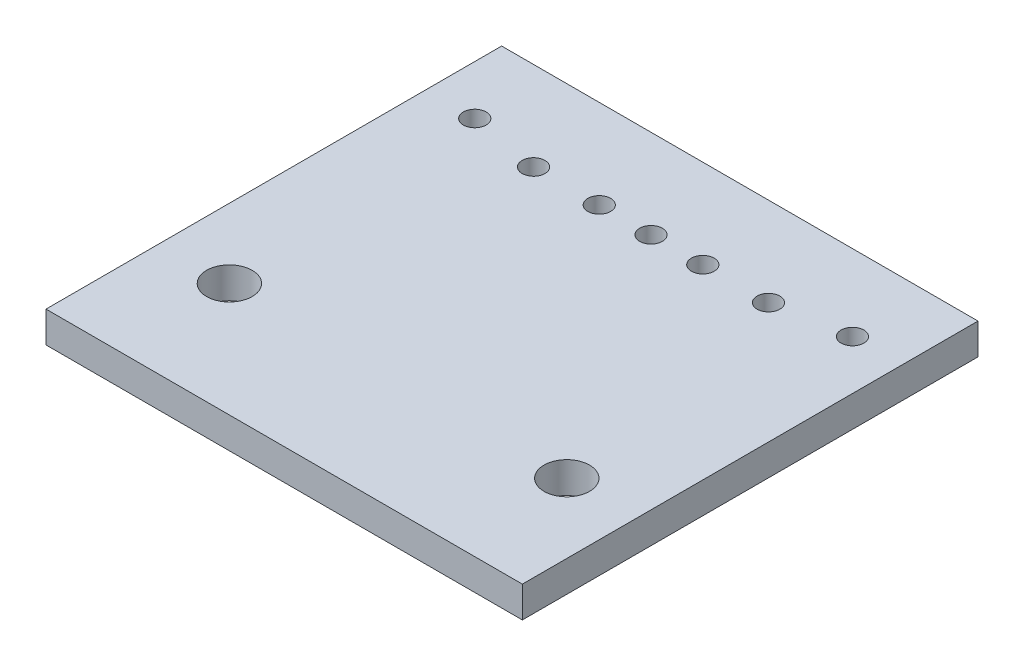
SolidWorks part; units mm, degrees
ref_plane "Front Plane" through (0, 0, 0) normal (0, 0, 1) x (1, 0, 0)
ref_plane "Top Plane" through (0, 0, 0) normal (0, 1, 0) x (1, 0, 0)
ref_plane "Right Plane" through (0, 0, 0) normal (1, 0, 0) x (0, 0, -1)
sketch "Sketch1" plane through (0, 0, 0) normal (0, 1, 0) x (1, 0, 0)
  line L1 (-11.5, -11) -> (11.5, -11)
  line L2 (-11.5, -11) -> (-11.5, 11)
  line L3 (-11.5, 11) -> (11.5, 11)
  line L4 (11.5, -11) -> (11.5, 11)
  line L5 (-11.5, -11) -> (11.5, 11) construction
  line L6 (-11.5, 11) -> (11.5, -11) construction
  point P0 (0, 0)
  dimension "D1" = 23
  dimension "D2" = 22
extrude "Boss-Extrude1" add sketch "Sketch1" along normal blind 1.5
sketch "Sketch2" plane through (0, 0, 0) normal (0, -1, 0) x (1, 0, 0)
  circle A0 centre (-8.1451, 5.5) radius 0.875 construction
  circle A1 centre (8.1451, 5.5) radius 0.875 construction
  circle A4 centre (-8.1451, 5.5) radius 0.875
  circle A5 centre (8.1451, 5.5) radius 0.875
  spline S0 degree 3 poles (-8.0835, -7.431) (-8.1588, -7.0042) (-8.2057, -6.866) (-8.3382, -6.6139) (-8.4259, -6.4966) (-8.6365, -6.3036) (-8.762, -6.2261) (-8.9642, -6.158) (-9.0356, -6.1427) (-9.1788, -6.1307) (-9.25, -6.1336) (-9.4629, -6.1699) (-9.5982, -6.2321) (-9.824, -6.4097) (-9.9158, -6.5248) (-10.0497, -6.7794) (-10.0923, -6.9184) (-10.1318, -7.2048) (-10.1286, -7.3483) (-10.0791, -7.6331) (-10.0337, -7.7687) (-9.9006, -8.024) (-9.8145, -8.1396) (-9.6041, -8.3341) (-9.4799, -8.4121) (-9.2737, -8.4821) (-9.2037, -8.4971) (-9.0612, -8.5095) (-8.9877, -8.5067) (-8.7754, -8.4707) (-8.6403, -8.4091) (-8.4131, -8.2308) (-8.321, -8.1151) (-8.12, -7.7325) (-8.0835, -7.431) (-8.1588, -7.0042) (-8.2057, -6.866) knots -0.125 -0.125 0 0 0.0625 0.0625 0.125 0.125 0.1875 0.1875 0.21875 0.21875 0.25 0.25 0.3125 0.3125 0.375 0.375 0.4375 0.4375 0.5 0.5 0.5625 0.5625 0.625 0.625 0.6875 0.6875 0.71875 0.71875 0.75 0.75 0.8125 0.8125 0.875 0.875 1 1 1.0625 1.0625 1.125 only from (-8.1337, -7.1465) to (-8.1337, -7.1465) construction
  spline S1 degree 3 poles (-4.6367, -6.8232) (-4.712, -6.3964) (-4.7588, -6.2582) (-4.8914, -6.0061) (-4.9791, -5.8889) (-5.1897, -5.6958) (-5.3152, -5.6183) (-5.5174, -5.5502) (-5.5888, -5.535) (-5.7319, -5.5229) (-5.8032, -5.5258) (-6.0161, -5.5621) (-6.1514, -5.6244) (-6.3772, -5.8019) (-6.469, -5.917) (-6.6029, -6.1717) (-6.6455, -6.3107) (-6.685, -6.597) (-6.6818, -6.7405) (-6.6322, -7.0253) (-6.5869, -7.1609) (-6.4538, -7.4162) (-6.3677, -7.5319) (-6.1573, -7.7264) (-6.0331, -7.8044) (-5.8269, -7.8744) (-5.7569, -7.8893) (-5.6144, -7.9017) (-5.5408, -7.8989) (-5.3286, -7.8629) (-5.1935, -7.8013) (-4.9663, -7.6231) (-4.8741, -7.5074) (-4.6732, -7.1248) (-4.6367, -6.8232) (-4.712, -6.3964) (-4.7588, -6.2582) knots -0.125 -0.125 0 0 0.0625 0.0625 0.125 0.125 0.1875 0.1875 0.21875 0.21875 0.25 0.25 0.3125 0.3125 0.375 0.375 0.4375 0.4375 0.5 0.5 0.5625 0.5625 0.625 0.625 0.6875 0.6875 0.71875 0.71875 0.75 0.75 0.8125 0.8125 0.875 0.875 1 1 1.0625 1.0625 1.125 only from (-4.6869, -6.5387) to (-4.6869, -6.5387) construction
  spline S2 degree 3 poles (8.1588, -7.0042) (8.1086, -7.2887) (8.1052, -7.4312) (8.1434, -7.7162) (8.1849, -7.8539) (8.3163, -8.1082) (8.4064, -8.2237) (8.5761, -8.3595) (8.6367, -8.3974) (8.7662, -8.4576) (8.8362, -8.48) (9.0476, -8.5186) (9.1954, -8.5069) (9.4695, -8.4173) (9.5955, -8.3403) (9.9149, -8.0501) (10.0524, -7.7785) (10.1279, -7.3564) (10.1318, -7.2099) (10.0942, -6.927) (10.0523, -6.7867) (9.9208, -6.5321) (9.8294, -6.4158) (9.6071, -6.2373) (9.4728, -6.1735) (9.1896, -6.1215) (9.0405, -6.1335) (8.7668, -6.2233) (8.6408, -6.3003) (8.4278, -6.4942) (8.34, -6.6109) (8.2051, -6.8667) (8.1588, -7.0042) (8.1086, -7.2887) (8.1052, -7.4312) knots -0.0625 -0.0625 0 0 0.0625 0.0625 0.125 0.125 0.1875 0.1875 0.21875 0.21875 0.25 0.25 0.3125 0.3125 0.375 0.375 0.5 0.5 0.5625 0.5625 0.625 0.625 0.6875 0.6875 0.75 0.75 0.8125 0.8125 0.875 0.875 0.9375 0.9375 1 1 1.0625 1.0625 1.125 only from (8.1337, -7.1465) to (8.1337, -7.1465) construction
  spline S3 degree 3 poles (4.737, -6.2542) (4.6618, -6.6809) (4.6586, -6.8268) (4.6969, -7.1091) (4.7392, -7.2493) (4.8711, -7.5027) (4.9625, -7.6185) (5.1292, -7.7516) (5.1911, -7.7904) (5.3215, -7.8506) (5.3895, -7.8723) (5.6019, -7.911) (5.7504, -7.8988) (6.0232, -7.8092) (6.1489, -7.7324) (6.3618, -7.5389) (6.4494, -7.4228) (6.5844, -7.1673) (6.6305, -7.0314) (6.6814, -6.7468) (6.6851, -6.6038) (6.6473, -6.3184) (6.606, -6.1803) (6.4748, -5.9256) (6.3848, -5.8098) (6.2149, -5.6735) (6.1543, -5.6355) (6.0246, -5.5751) (5.9546, -5.5526) (5.7428, -5.5138) (5.5948, -5.5255) (5.3203, -5.6153) (5.1942, -5.6925) (4.8745, -5.9833) (4.737, -6.2542) (4.6618, -6.6809) (4.6586, -6.8268) knots -0.125 -0.125 0 0 0.0625 0.0625 0.125 0.125 0.1875 0.1875 0.21875 0.21875 0.25 0.25 0.3125 0.3125 0.375 0.375 0.4375 0.4375 0.5 0.5 0.5625 0.5625 0.625 0.625 0.6875 0.6875 0.71875 0.71875 0.75 0.75 0.8125 0.8125 0.875 0.875 1 1 1.0625 1.0625 1.125 only from (4.6869, -6.5387) to (4.6869, -6.5387) construction
  spline S4 degree 3 poles (-8.0835, -7.431) (-8.1588, -7.0042) (-8.2057, -6.866) (-8.3382, -6.6139) (-8.4259, -6.4966) (-8.6365, -6.3036) (-8.762, -6.2261) (-8.9642, -6.158) (-9.0356, -6.1427) (-9.1788, -6.1307) (-9.25, -6.1336) (-9.4629, -6.1699) (-9.5982, -6.2321) (-9.824, -6.4097) (-9.9158, -6.5248) (-10.0497, -6.7794) (-10.0923, -6.9184) (-10.1318, -7.2048) (-10.1286, -7.3483) (-10.0791, -7.6331) (-10.0337, -7.7687) (-9.9006, -8.024) (-9.8145, -8.1396) (-9.6041, -8.3341) (-9.4799, -8.4121) (-9.2737, -8.4821) (-9.2037, -8.4971) (-9.0612, -8.5095) (-8.9877, -8.5067) (-8.7754, -8.4707) (-8.6403, -8.4091) (-8.4131, -8.2308) (-8.321, -8.1151) (-8.12, -7.7325) (-8.0835, -7.431) (-8.1588, -7.0042) (-8.2057, -6.866) knots -0.125 -0.125 0 0 0.0625 0.0625 0.125 0.125 0.1875 0.1875 0.21875 0.21875 0.25 0.25 0.3125 0.3125 0.375 0.375 0.4375 0.4375 0.5 0.5 0.5625 0.5625 0.625 0.625 0.6875 0.6875 0.71875 0.71875 0.75 0.75 0.8125 0.8125 0.875 0.875 1 1 1.0625 1.0625 1.125 only from (-8.1337, -7.1465) to (-8.1337, -7.1465)
  spline S5 degree 3 poles (-4.6367, -6.8232) (-4.712, -6.3964) (-4.7588, -6.2582) (-4.8914, -6.0061) (-4.9791, -5.8889) (-5.1897, -5.6958) (-5.3152, -5.6183) (-5.5174, -5.5502) (-5.5888, -5.535) (-5.7319, -5.5229) (-5.8032, -5.5258) (-6.0161, -5.5621) (-6.1514, -5.6244) (-6.3772, -5.8019) (-6.469, -5.917) (-6.6029, -6.1717) (-6.6455, -6.3107) (-6.685, -6.597) (-6.6818, -6.7405) (-6.6322, -7.0253) (-6.5869, -7.1609) (-6.4538, -7.4162) (-6.3677, -7.5319) (-6.1573, -7.7264) (-6.0331, -7.8044) (-5.8269, -7.8744) (-5.7569, -7.8893) (-5.6144, -7.9017) (-5.5408, -7.8989) (-5.3286, -7.8629) (-5.1935, -7.8013) (-4.9663, -7.6231) (-4.8741, -7.5074) (-4.6732, -7.1248) (-4.6367, -6.8232) (-4.712, -6.3964) (-4.7588, -6.2582) knots -0.125 -0.125 0 0 0.0625 0.0625 0.125 0.125 0.1875 0.1875 0.21875 0.21875 0.25 0.25 0.3125 0.3125 0.375 0.375 0.4375 0.4375 0.5 0.5 0.5625 0.5625 0.625 0.625 0.6875 0.6875 0.71875 0.71875 0.75 0.75 0.8125 0.8125 0.875 0.875 1 1 1.0625 1.0625 1.125 only from (-4.6869, -6.5387) to (-4.6869, -6.5387)
  spline S6 degree 3 poles (8.1588, -7.0042) (8.1086, -7.2887) (8.1052, -7.4312) (8.1434, -7.7162) (8.1849, -7.8539) (8.3163, -8.1082) (8.4064, -8.2237) (8.5761, -8.3595) (8.6367, -8.3974) (8.7662, -8.4576) (8.8362, -8.48) (9.0476, -8.5186) (9.1954, -8.5069) (9.4695, -8.4173) (9.5955, -8.3403) (9.9149, -8.0501) (10.0524, -7.7785) (10.1279, -7.3564) (10.1318, -7.2099) (10.0942, -6.927) (10.0523, -6.7867) (9.9208, -6.5321) (9.8294, -6.4158) (9.6071, -6.2373) (9.4728, -6.1735) (9.1896, -6.1215) (9.0405, -6.1335) (8.7668, -6.2233) (8.6408, -6.3003) (8.4278, -6.4942) (8.34, -6.6109) (8.2051, -6.8667) (8.1588, -7.0042) (8.1086, -7.2887) (8.1052, -7.4312) knots -0.0625 -0.0625 0 0 0.0625 0.0625 0.125 0.125 0.1875 0.1875 0.21875 0.21875 0.25 0.25 0.3125 0.3125 0.375 0.375 0.5 0.5 0.5625 0.5625 0.625 0.625 0.6875 0.6875 0.75 0.75 0.8125 0.8125 0.875 0.875 0.9375 0.9375 1 1 1.0625 1.0625 1.125 only from (8.1337, -7.1465) to (8.1337, -7.1465)
  spline S7 degree 3 poles (4.737, -6.2542) (4.6618, -6.6809) (4.6586, -6.8268) (4.6969, -7.1091) (4.7392, -7.2493) (4.8711, -7.5027) (4.9625, -7.6185) (5.1292, -7.7516) (5.1911, -7.7904) (5.3215, -7.8506) (5.3895, -7.8723) (5.6019, -7.911) (5.7504, -7.8988) (6.0232, -7.8092) (6.1489, -7.7324) (6.3618, -7.5389) (6.4494, -7.4228) (6.5844, -7.1673) (6.6305, -7.0314) (6.6814, -6.7468) (6.6851, -6.6038) (6.6473, -6.3184) (6.606, -6.1803) (6.4748, -5.9256) (6.3848, -5.8098) (6.2149, -5.6735) (6.1543, -5.6355) (6.0246, -5.5751) (5.9546, -5.5526) (5.7428, -5.5138) (5.5948, -5.5255) (5.3203, -5.6153) (5.1942, -5.6925) (4.8745, -5.9833) (4.737, -6.2542) (4.6618, -6.6809) (4.6586, -6.8268) knots -0.125 -0.125 0 0 0.0625 0.0625 0.125 0.125 0.1875 0.1875 0.21875 0.21875 0.25 0.25 0.3125 0.3125 0.375 0.375 0.4375 0.4375 0.5 0.5 0.5625 0.5625 0.625 0.625 0.6875 0.6875 0.71875 0.71875 0.75 0.75 0.8125 0.8125 0.875 0.875 1 1 1.0625 1.0625 1.125 only from (4.6869, -6.5387) to (4.6869, -6.5387)
sketch "Sketch3" plane through (0, 1.5, 0) normal (0, 1, 0) x (1, 0, 0)
  line L0 (-8.1337, 7.1465) -> (-10.1033, 7.4941) construction
  line L1 (-4.6869, 6.5387) -> (-6.6564, 6.8863) construction
  line L2 (4.6869, 6.5387) -> (6.6565, 6.8857) construction
  line L3 (8.1337, 7.1465) -> (10.1033, 7.494) construction
  line L4 (-5.6717, 6.7125) -> (5.6717, 6.7122) construction
  circle A2 centre (8.1451, -5.5) radius 1.1
  circle A3 centre (-8.1451, -5.5) radius 1.1
  circle A4 centre (-9.1185, 7.3203) radius 0.55
  circle A5 centre (-5.6717, 6.7125) radius 0.55
  circle A6 centre (5.6717, 6.7122) radius 0.55
  circle A7 centre (9.1185, 7.3202) radius 0.55
  circle A8 centre (0, 6.7123) radius 0.55
  circle A9 centre (-2.5, 6.7124) radius 0.55
  circle A10 centre (2.5, 6.7123) radius 0.55
  spline S0 degree 3 poles (-8.1588, 7.0042) (-8.0835, 7.431) (-8.12, 7.7325) (-8.321, 8.1151) (-8.4131, 8.2308) (-8.6403, 8.4091) (-8.7754, 8.4707) (-8.9877, 8.5067) (-9.0612, 8.5095) (-9.2037, 8.4971) (-9.2737, 8.4821) (-9.4799, 8.4121) (-9.6041, 8.3341) (-9.8145, 8.1396) (-9.9006, 8.024) (-10.0337, 7.7687) (-10.0791, 7.6331) (-10.1286, 7.3483) (-10.1318, 7.2048) (-10.0923, 6.9184) (-10.0497, 6.7794) (-9.9158, 6.5248) (-9.824, 6.4097) (-9.5982, 6.2321) (-9.4629, 6.1699) (-9.25, 6.1336) (-9.1788, 6.1307) (-9.0356, 6.1427) (-8.9642, 6.158) (-8.762, 6.2261) (-8.6365, 6.3036) (-8.4259, 6.4966) (-8.3382, 6.6139) (-8.2057, 6.866) (-8.1588, 7.0042) (-8.0835, 7.431) (-8.12, 7.7325) knots -0.0625 -0.0625 0 0 0.125 0.125 0.1875 0.1875 0.25 0.25 0.28125 0.28125 0.3125 0.3125 0.375 0.375 0.4375 0.4375 0.5 0.5 0.5625 0.5625 0.625 0.625 0.6875 0.6875 0.75 0.75 0.78125 0.78125 0.8125 0.8125 0.875 0.875 0.9375 0.9375 1 1 1.125 1.125 1.1875 only from (-8.1337, 7.1465) to (-8.1337, 7.1465) construction
  spline S1 degree 3 poles (-4.712, 6.3964) (-4.6367, 6.8232) (-4.6732, 7.1248) (-4.8741, 7.5074) (-4.9663, 7.6231) (-5.1935, 7.8013) (-5.3286, 7.8629) (-5.5408, 7.8989) (-5.6144, 7.9017) (-5.7569, 7.8893) (-5.8269, 7.8744) (-6.0331, 7.8044) (-6.1573, 7.7264) (-6.3677, 7.5319) (-6.4538, 7.4162) (-6.5869, 7.1609) (-6.6322, 7.0253) (-6.6818, 6.7405) (-6.685, 6.597) (-6.6455, 6.3107) (-6.6029, 6.1717) (-6.469, 5.917) (-6.3772, 5.8019) (-6.1514, 5.6244) (-6.0161, 5.5621) (-5.8032, 5.5258) (-5.7319, 5.5229) (-5.5888, 5.535) (-5.5174, 5.5502) (-5.3152, 5.6183) (-5.1897, 5.6958) (-4.9791, 5.8889) (-4.8914, 6.0061) (-4.7588, 6.2582) (-4.712, 6.3964) (-4.6367, 6.8232) (-4.6732, 7.1248) knots -0.0625 -0.0625 0 0 0.125 0.125 0.1875 0.1875 0.25 0.25 0.28125 0.28125 0.3125 0.3125 0.375 0.375 0.4375 0.4375 0.5 0.5 0.5625 0.5625 0.625 0.625 0.6875 0.6875 0.75 0.75 0.78125 0.78125 0.8125 0.8125 0.875 0.875 0.9375 0.9375 1 1 1.125 1.125 1.1875 only from (-4.6869, 6.5387) to (-4.6869, 6.5387) construction
  spline S2 degree 3 poles (4.6618, 6.6809) (4.737, 6.2542) (4.8745, 5.9833) (5.1942, 5.6925) (5.3203, 5.6153) (5.5948, 5.5255) (5.7428, 5.5138) (5.9546, 5.5526) (6.0246, 5.5751) (6.1543, 5.6355) (6.2149, 5.6735) (6.3848, 5.8098) (6.4748, 5.9256) (6.606, 6.1803) (6.6473, 6.3184) (6.6851, 6.6038) (6.6814, 6.7468) (6.6305, 7.0314) (6.5844, 7.1673) (6.4494, 7.4228) (6.3618, 7.5389) (6.1489, 7.7324) (6.0232, 7.8092) (5.7504, 7.8988) (5.6019, 7.911) (5.3895, 7.8723) (5.3215, 7.8506) (5.1911, 7.7904) (5.1292, 7.7516) (4.9625, 7.6185) (4.8711, 7.5027) (4.7392, 7.2493) (4.6969, 7.1091) (4.6586, 6.8268) (4.6618, 6.6809) (4.737, 6.2542) (4.8745, 5.9833) knots -0.0625 -0.0625 0 0 0.125 0.125 0.1875 0.1875 0.25 0.25 0.28125 0.28125 0.3125 0.3125 0.375 0.375 0.4375 0.4375 0.5 0.5 0.5625 0.5625 0.625 0.625 0.6875 0.6875 0.75 0.75 0.78125 0.78125 0.8125 0.8125 0.875 0.875 0.9375 0.9375 1 1 1.125 1.125 1.1875 only from (4.6869, 6.5387) to (4.6869, 6.5387) construction
  spline S3 degree 3 poles (8.1086, 7.2887) (8.1588, 7.0042) (8.2051, 6.8667) (8.34, 6.6109) (8.4278, 6.4942) (8.6408, 6.3003) (8.7668, 6.2233) (9.0405, 6.1335) (9.1896, 6.1215) (9.4728, 6.1735) (9.6071, 6.2373) (9.8294, 6.4158) (9.9208, 6.5321) (10.0523, 6.7867) (10.0942, 6.927) (10.1318, 7.2099) (10.1279, 7.3564) (10.0524, 7.7785) (9.9149, 8.0501) (9.5955, 8.3403) (9.4695, 8.4173) (9.1954, 8.5069) (9.0476, 8.5186) (8.8362, 8.48) (8.7662, 8.4576) (8.6367, 8.3974) (8.5761, 8.3595) (8.4064, 8.2237) (8.3163, 8.1082) (8.1849, 7.8539) (8.1434, 7.7162) (8.1052, 7.4312) (8.1086, 7.2887) (8.1588, 7.0042) (8.2051, 6.8667) knots -0.0625 -0.0625 0 0 0.0625 0.0625 0.125 0.125 0.1875 0.1875 0.25 0.25 0.3125 0.3125 0.375 0.375 0.4375 0.4375 0.5 0.5 0.625 0.625 0.6875 0.6875 0.75 0.75 0.78125 0.78125 0.8125 0.8125 0.875 0.875 0.9375 0.9375 1 1 1.0625 1.0625 1.125 only from (8.1337, 7.1465) to (8.1337, 7.1465) construction
  dimension "D6" = 1.1
  dimension "D7" = 1.1
  dimension "D1" = 2
  dimension "D2" = 2
  dimension "D3" = 2
  dimension "D4" = 2
  dimension "D8" = 2.5
  dimension "D9" = 2.5
extrude "Cut-Extrude1" cut sketch "Sketch3" against normal through all contours A3 | A4 | A5 | A9 | A8 | A10 | A6 | A7 | A2
sketch "Sketch4" plane through (0, 0, 0) normal (0, -1, 0) x (1, 0, 0)
  line L0 (2.5, -6.7123) -> (5.6717, -6.7122)
  line L1 (9.1185, -7.3202) -> (9.1185, 0)
  line L2 (9.1185, 0) -> (0, 0)
  line L3 (0, 0) -> (0, -6.7123)
  line L4 (0, 0) -> (-9.1185, 0)
  line L5 (-9.1185, 0) -> (-9.1185, -7.3203)
  line L6 (-5.6717, -6.7125) -> (-2.5, -6.7124)
